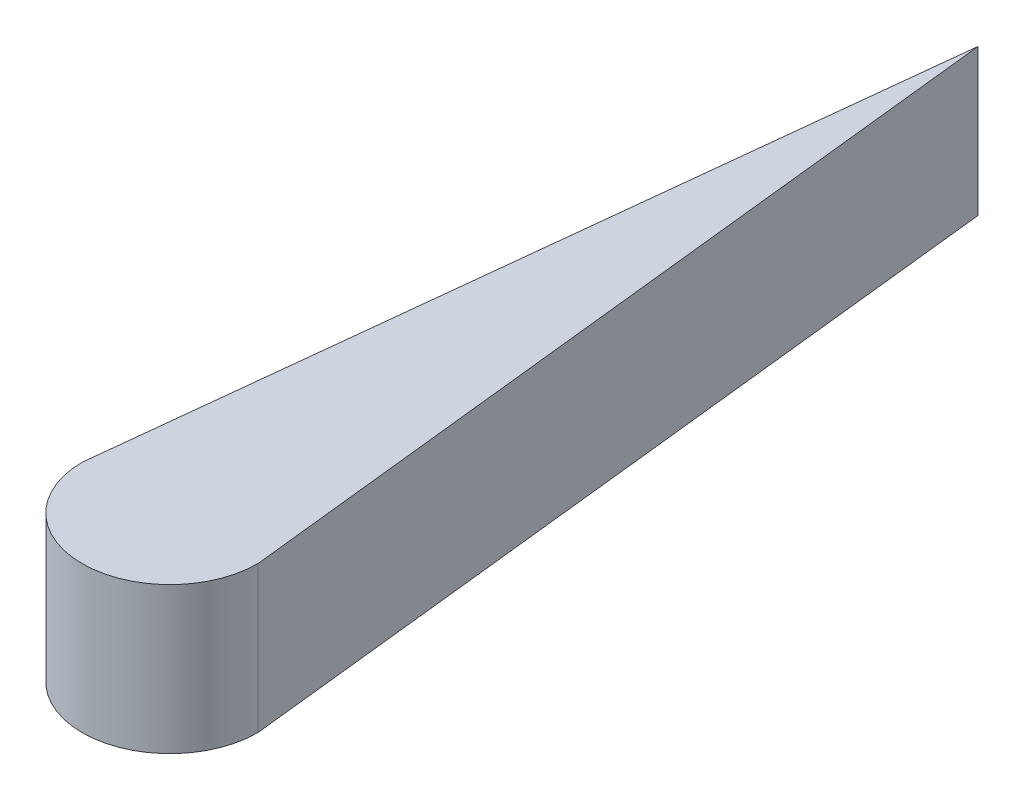
SolidWorks part; units mm, degrees
ref_plane "Front Plane" through (0, 0, 0) normal (0, 0, 1) x (1, 0, 0)
ref_plane "Top Plane" through (0, 0, 0) normal (0, 1, 0) x (1, 0, 0)
ref_plane "Right Plane" through (0, 0, 0) normal (1, 0, 0) x (0, 0, -1)
sketch "Sketch1" plane through (0, 0, 0) normal (0, 1, 0) x (1, 0, 0)
  line L0 (0, 0) -> (0, 38.862)
  line L1 (0, 38.862) -> (-3.81, 3.81)
  line L2 (0, 38.862) -> (3.81, 3.81)
  circle A1 centre (0, 3.81) radius 3.81
  dimension "D2" = 7.62
  dimension "D1" = 38.862
extrude "Boss-Extrude1" add sketch "Sketch1" along normal blind 6.35 contours A1 L0 L1 | A1 L2 L0 | L0 A1 L1 | L0 A1 L2
